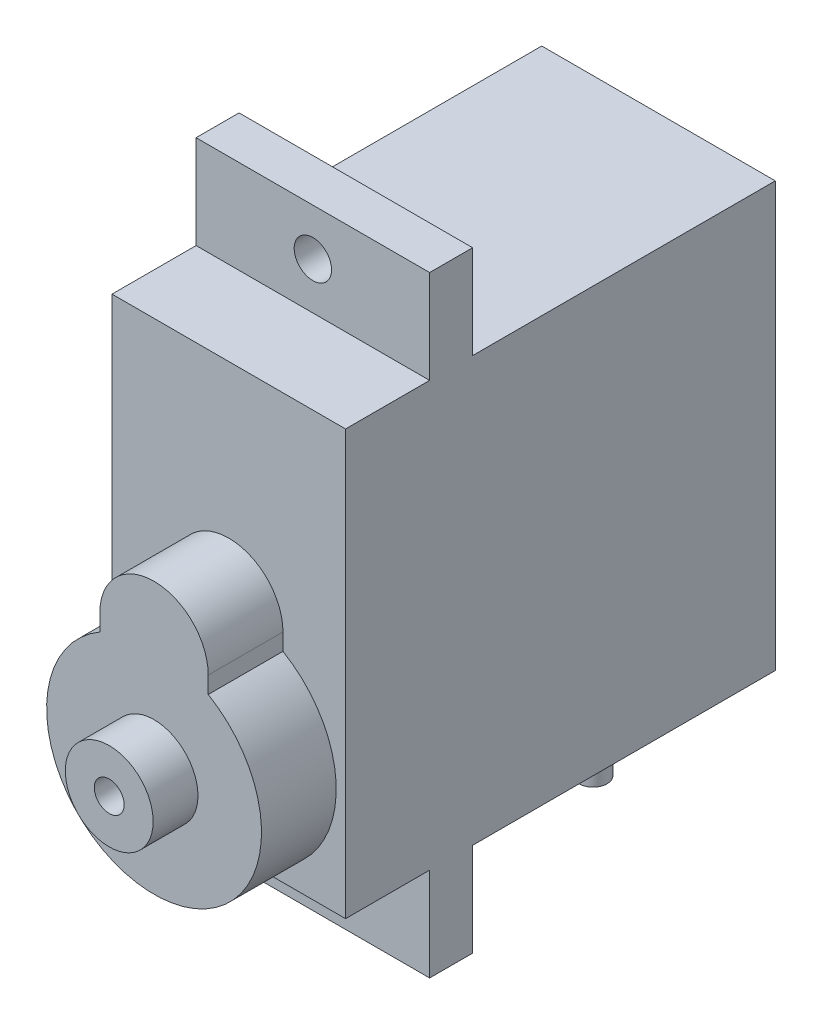
SolidWorks part; units mm, degrees
ref_plane "Alzado" through (0, 0, 0) normal (0, 0, 1) x (1, 0, 0)
ref_plane "Planta" through (0, 0, 0) normal (0, 1, 0) x (1, 0, 0)
ref_plane "Vista lateral" through (0, 0, 0) normal (1, 0, 0) x (0, 0, -1)
sketch "Croquis1" plane through (0, 0, 0) normal (0, 0, 1) x (1, 0, 0)
  line L1 (-6.25, -11.35) -> (6.25, -11.35)
  line L2 (-6.25, -11.35) -> (-6.25, 11.35)
  line L3 (-6.25, 11.35) -> (6.25, 11.35)
  line L4 (6.25, -11.35) -> (6.25, 11.35)
  line L5 (-6.25, -11.35) -> (6.25, 11.35) construction
  line L6 (-6.25, 11.35) -> (6.25, -11.35) construction
  point P0 (0, 0)
  dimension "D1" = 22.7
  dimension "D2" = 12.5
extrude "Saliente-Extruir1" add sketch "Croquis1" along normal blind 23
sketch "Croquis2" plane through (0, 0, 23) normal (0, 0, 1) x (1, 0, 0)
  line L0 (-6.25, -11.35) -> (6.25, -11.35) construction
  line L1 (2.9, 0.2651) -> (2.9, -0.6349)
  line L2 (-2.9, 0.2651) -> (-2.9, -0.6349)
  line L3 (0, 0) -> (0, 11.35) construction
  line L4 (6.25, 11.35) -> (-6.25, 11.35) construction
  arc A0 (-2.9, -0.6349) -> (2.9, -0.6349) centre (0, -5.6) ccw
  arc A1 (2.9, 0.2651) -> (-2.9, 0.2651) centre (0, 0.2651) ccw
  dimension "D1" = 11.5
  dimension "D2" = 5.8
  dimension "D3" = 0.9
extrude "Saliente-Extruir2" add sketch "Croquis2" along normal blind 4
sketch "Croquis3" plane through (0, 0, 0) normal (1, 0, 0) x (0, 0, -1)
  line L0 (-23, 11.35) -> (0, 11.35) construction
  line L1 (-16.2, 11.35) -> (-18.5, 11.35)
  line L2 (-16.2, 11.35) -> (-16.2, 16.35)
  line L3 (-16.2, 16.35) -> (-18.5, 16.35)
  line L4 (-18.5, 11.35) -> (-18.5, 16.35)
  line L5 (-23, -11.35) -> (-23, 11.35) construction
  line L6 (0, 0) -> (-23, 0) construction
  line L7 (-18.5, -11.35) -> (-18.5, -16.35)
  line L8 (-16.2, -11.35) -> (-16.2, -16.35)
  line L9 (-16.2, -11.35) -> (-18.5, -11.35)
  line L10 (-16.2, -16.35) -> (-18.5, -16.35)
  dimension "D1" = 4.5
  dimension "D2" = 2.3
  dimension "D3" = 5
extrude "Saliente-Extruir3" add sketch "Croquis3" along normal mid plane 12.5
sketch "Croquis4" plane through (0, 0, 18.5) normal (0, 0, 1) x (1, 0, 0)
  line L0 (0, 16.35) -> (0, 11.35) construction
  line L1 (6.25, 16.35) -> (-6.25, 16.35) construction
  line L2 (6.25, 11.35) -> (-6.25, 11.35) construction
  line L3 (-6.25, 0) -> (6.25, 0) construction
  line L4 (-6.25, 11.35) -> (-6.25, -11.35) construction
  line L5 (6.25, -11.35) -> (6.25, 11.35) construction
  circle A0 centre (0, 13.85) radius 1
  circle A1 centre (0, -13.85) radius 1
  dimension "D1" = 2
extrude "Cortar-Extruir1" cut sketch "Croquis4" against normal up to next
sketch "Croquis5" plane through (0, 0, 0) normal (0, 0, -1) x (-1, 0, 0)
  line L0 (-6.25, -11.35) -> (6.25, -11.35) construction
  line L1 (-2, -11.35) -> (2, -11.35)
  line L2 (-2, -11.35) -> (-2, -16.35)
  line L3 (-2, -16.35) -> (2, -16.35)
  line L4 (2, -11.35) -> (2, -16.35)
  line L5 (0, -11.35) -> (0, 0) construction
  line L6 (-6.25, -16.35) -> (6.25, -16.35) construction
  dimension "D1" = 4
extrude "Saliente-Extruir4" add sketch "Croquis5" against normal blind 1.5 from offset 4 offset against normal yes
sketch "Croquis6" plane through (0, 0, 27) normal (0, 0, 1) x (1, 0, 0)
  circle A0 centre (0, -5.6) radius 2.35
  circle A1 centre (0, -5.6) radius 0.8
  dimension "D1" = 4.7
  dimension "D2" = 1.6
extrude "Saliente-Extruir5" add sketch "Croquis6" along normal blind 2.4
sketch "Sketch1" plane through (0, -16.35, 0) normal (0, -1, 0) x (1, 0, 0)
  line L0 (2, 5.5) -> (-2, 5.5) construction
  line L1 (-2, 4) -> (2, 4) construction
  line L2 (2, 5.5) -> (2, 4) construction
  line L3 (0, 5.5) -> (0, 0) construction
  line L4 (-2, 5.5) -> (2, 5.5) construction
  line L6 (-2.2574, 3.6981) -> (2.2574, 3.6981)
  line L7 (-2.2574, 3.6981) -> (-2.2574, 5.8019)
  line L8 (-2.2574, 5.8019) -> (2.2574, 5.8019)
  line L9 (2.2574, 3.6981) -> (2.2574, 5.8019)
  line L10 (-2.2574, 3.6981) -> (2.2574, 5.8019) construction
  line L11 (-2.2574, 5.8019) -> (2.2574, 3.6981) construction
  arc A0 (-0.625, 4.3354) -> (-0.625, 5.1646) centre (-1.25, 4.75) cw
  arc A1 (-0.625, 4.3354) -> (0.625, 4.3354) centre (0, 4.75) ccw
  arc A2 (0.625, 4.3354) -> (0.625, 5.1646) centre (1.25, 4.75) ccw
  arc A3 (0.625, 5.1646) -> (-0.625, 5.1646) centre (0, 4.75) ccw
extrude "Cut-Extrude2" cut sketch "Sketch1" against normal up to surface (5 mm away) up to face at (0, -11.35, 8.1)
